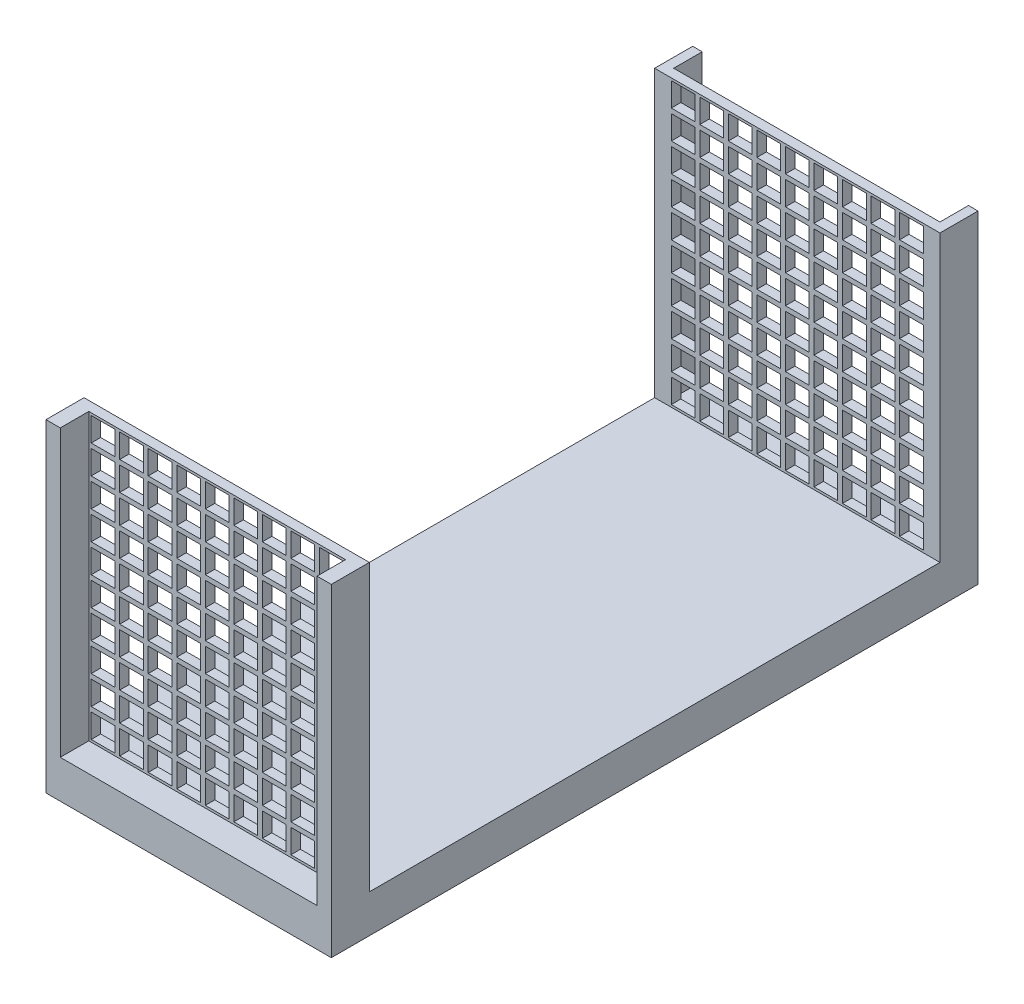
SolidWorks part; units mm, degrees
ref_plane "Front Plane" through (0, 0, 0) normal (0, 0, 1) x (1, 0, 0)
ref_plane "Top Plane" through (0, 0, 0) normal (0, 1, 0) x (1, 0, 0)
ref_plane "Right Plane" through (0, 0, 0) normal (1, 0, 0) x (0, 0, -1)
sketch "Sketch1" plane through (0, 0, 0) normal (0, 0, 1) x (1, 0, 0)
  line L1 (7.5, -8.5) -> (-7.5, -8.5)
  line L2 (7.5, -8.5) -> (7.5, 8.5)
  line L3 (7.5, 8.5) -> (-7.5, 8.5)
  line L4 (-7.5, -8.5) -> (-7.5, 8.5)
  line L5 (7.5, -8.5) -> (-7.5, 8.5) construction
  line L6 (7.5, 8.5) -> (-7.5, -8.5) construction
  point P0 (0, 0)
  dimension "D1" = 15
  dimension "D2" = 17
extrude "Boss-Extrude1" add sketch "Sketch1" along normal blind 34
sketch "Sketch2" plane through (7.5, 0, 0) normal (1, 0, 0) x (0, 0, -1)
  line L0 (-34, 8.5) -> (0, 8.5) construction
  line L1 (-32, 8.5) -> (-2, 8.5)
  line L2 (-32, 8.5) -> (-32, -6.5)
  line L3 (-32, -6.5) -> (-2, -6.5)
  line L4 (-2, 8.5) -> (-2, -6.5)
  line L5 (-34, -8.5) -> (-34, 8.5) construction
  line L6 (-34, -8.5) -> (0, -8.5) construction
  line L7 (0, -8.5) -> (0, 8.5) construction
  dimension "D1" = 2
  dimension "D2" = 2
  dimension "D3" = 2
extrude "Cut-Extrude1" cut sketch "Sketch2" against normal up to next
sketch "Sketch3" plane through (0, 0, 34) normal (0, 0, 1) x (1, 0, 0)
  line L0 (7.5, 8.5) -> (-7.5, 8.5) construction
  line L1 (-6.75, 8.5) -> (6.75, 8.5)
  line L2 (-6.75, 8.5) -> (-6.75, -6.5)
  line L3 (-6.75, -6.5) -> (6.75, -6.5)
  line L4 (6.75, 8.5) -> (6.75, -6.5)
  line L5 (-7.5, 8.5) -> (-7.5, -8.5) construction
  line L7 (-7.5, -8.5) -> (7.5, -8.5) construction
  line L8 (7.5, 8.5) -> (6.75, 8.5) construction
  line L9 (-6.75, 8.5) -> (-7.5, 8.5) construction
  dimension "D1" = 0.75
  dimension "D3" = 2
extrude "Cut-Extrude2" cut sketch "Sketch3" against normal blind 1.5
sketch "Sketch4" plane through (0, 0, 32.5) normal (0, 0, 1) x (1, 0, 0)
  line L1 (-6.625, 8.375) -> (-5.375, 8.375)
  line L2 (-6.625, 8.375) -> (-6.625, 7.125)
  line L3 (-6.625, 7.125) -> (-5.375, 7.125)
  line L4 (-5.375, 8.375) -> (-5.375, 7.125)
  line L5 (-6.75, 8.5) -> (-6.625, 8.5) construction
  line L6 (-6.75, 8.5) -> (-6.75, 8.375) construction
  line L7 (-6.75, 8.375) -> (-6.625, 8.375) construction
  line L8 (-6.625, 8.5) -> (-6.625, 8.375) construction
  dimension "D1" = 0.125
  dimension "D3" = 1.25
extrude "Cut-Extrude3" cut sketch "Sketch4" against normal through all
pattern_linear "LPattern1" count 9 spacing 1.5 along (1, 0, 0) count 10 spacing 1.5 along (0, -1, 0) of "Cut-Extrude3"
sketch "Sketch5" plane through (0, 0, 0) normal (0, 0, -1) x (-1, 0, 0)
  line L0 (-7.5, 8.5) -> (7.5, 8.5) construction
  line L1 (-7, 8.5) -> (7, 8.5)
  line L2 (-7, 8.5) -> (-7, -6.5)
  line L3 (-7, -6.5) -> (7, -6.5)
  line L4 (7, 8.5) -> (7, -6.5)
  line L5 (-7, 8.5) -> (-7.5, 8.5) construction
  line L6 (-7.5, 8.5) -> (7, 8.5) construction
  line L7 (-7.5, -8.5) -> (-7.5, 8.5) construction
  line L8 (7, 8.5) -> (7.5, 8.5) construction
  line L9 (7.5, -8.5) -> (-7.5, -8.5) construction
  dimension "D1" = 0.5
  dimension "D2" = 2
extrude "Cut-Extrude4" cut sketch "Sketch5" against normal blind 1.5
